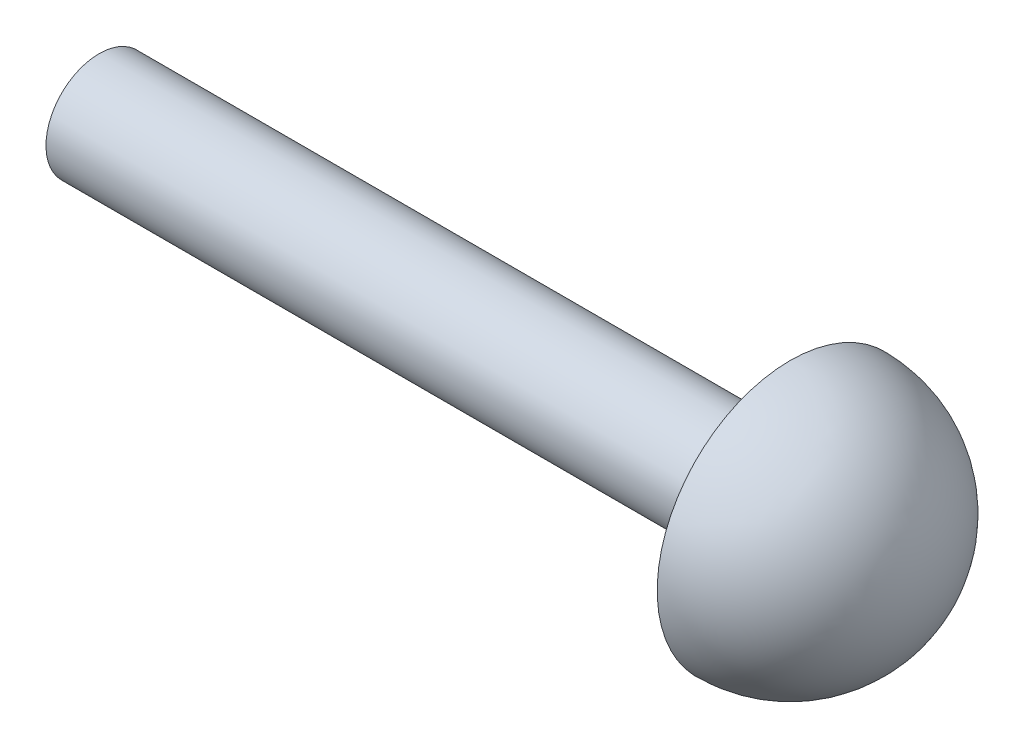
SolidWorks part; units mm, degrees
ref_plane "前基準面" through (0, 0, 0) normal (0, 0, 1) x (1, 0, 0)
ref_plane "上基準面" through (0, 0, 0) normal (0, 1, 0) x (1, 0, 0)
ref_plane "右基準面" through (0, 0, 0) normal (1, 0, 0) x (0, 0, -1)
sketch "草圖1" plane through (0, 0, 0) normal (0, 0, 1) x (1, 0, 0)
  line L0 (0, 0) -> (-26, 0)
  line L1 (-26, 0) -> (-26, 2)
  line L2 (-26, 2) -> (0, 2)
  line L3 (0, 2) -> (0, 5)
  line L4 (0, 0) -> (5, 0)
  arc A0 (5, 0) -> (0, 5) centre (0, 0) ccw
  dimension "D1" = 10
  dimension "D2" = 26
  dimension "D3" = 2
revolve "旋轉1" add sketch "草圖1" angle 360 about L0
